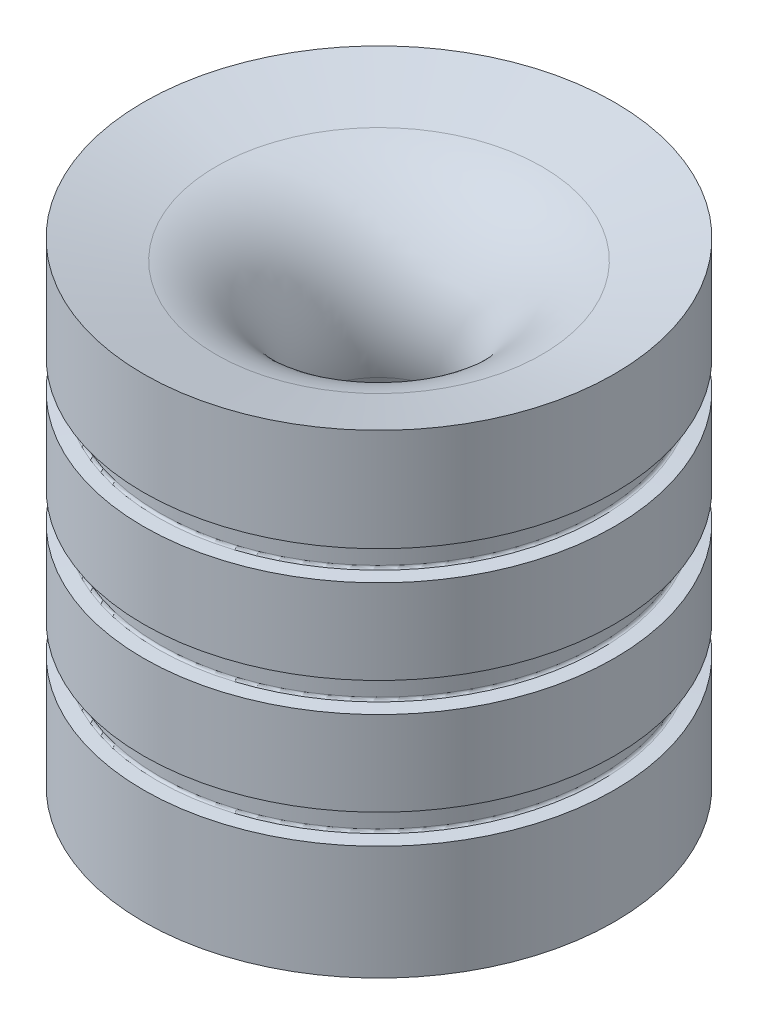
SolidWorks part; units mm, degrees
material "C (Graphite)"
ref_plane "Front Plane" through (0, 0, 0) normal (0, 0, 1) x (1, 0, 0)
ref_plane "Top Plane" through (0, 0, 0) normal (0, 1, 0) x (1, 0, 0)
ref_plane "Right Plane" through (0, 0, 0) normal (1, 0, 0) x (0, 0, -1)
sketch "Sketch1" plane through (0, 0, 0) normal (0, 0, 1) x (1, 0, 0)
  line L0 (0, -55) -> (0, 55) construction
  line L1 (41.275, 83.1623) -> (41.275, 0)
  line L2 (41.275, 83.1623) -> (28.556, 79.7543)
  line L3 (41.275, 0) -> (27.15, 0)
  line L4 (27.15, 0) -> (12.9996, 52.8099)
  line L5 (0, 11.2039) -> (0, 47.7588) construction
  arc A0 (12.9996, 52.8099) -> (28.556, 79.7543) centre (34.25, 58.5039) cw
  dimension "D6" = 34.25
  dimension "D3" = 22
  dimension "D1" = 41.275
  dimension "D2" = 27.15
  dimension "D4" = 105
  dimension "D5" = 75
revolve "Revolve1" add sketch "Sketch1" angle 360 about L5
ref_plane "Plane1" through (0, 11.2039, 0) normal (-1, 0, 0) x (0, 0, -1)
sketch "Sketch3" plane through (0, 11.2039, 0) normal (-1, 0, 0) x (0, 0, -1)
  line L0 (38.8614, -9.0151) -> (41.3639, -8.7961)
  line L1 (41.3639, -8.7961) -> (41.3639, -13.9838)
  line L2 (41.3639, -13.9838) -> (38.8614, -13.7649)
  line L3 (38.4556, -13.322) -> (38.4556, -9.4579)
  line L4 (0, 50) -> (0, -50) construction
  line L5 (41.275, 11.2039) -> (-41.275, 11.2039) construction
  arc A0 (38.8614, -13.7649) -> (38.4556, -13.322) centre (38.9001, -13.322) cw
  arc A1 (38.4556, -9.4579) -> (38.8614, -9.0151) centre (38.9001, -9.4579) cw
  dimension "D1" = 20
revolve "Groove for AS 568-234, O-Ring1" cut sketch "Sketch3"
pattern_linear "LPattern1" count 3 spacing 20 along (0, 1, 0) of "Groove for AS 568-234, O-Ring1"
